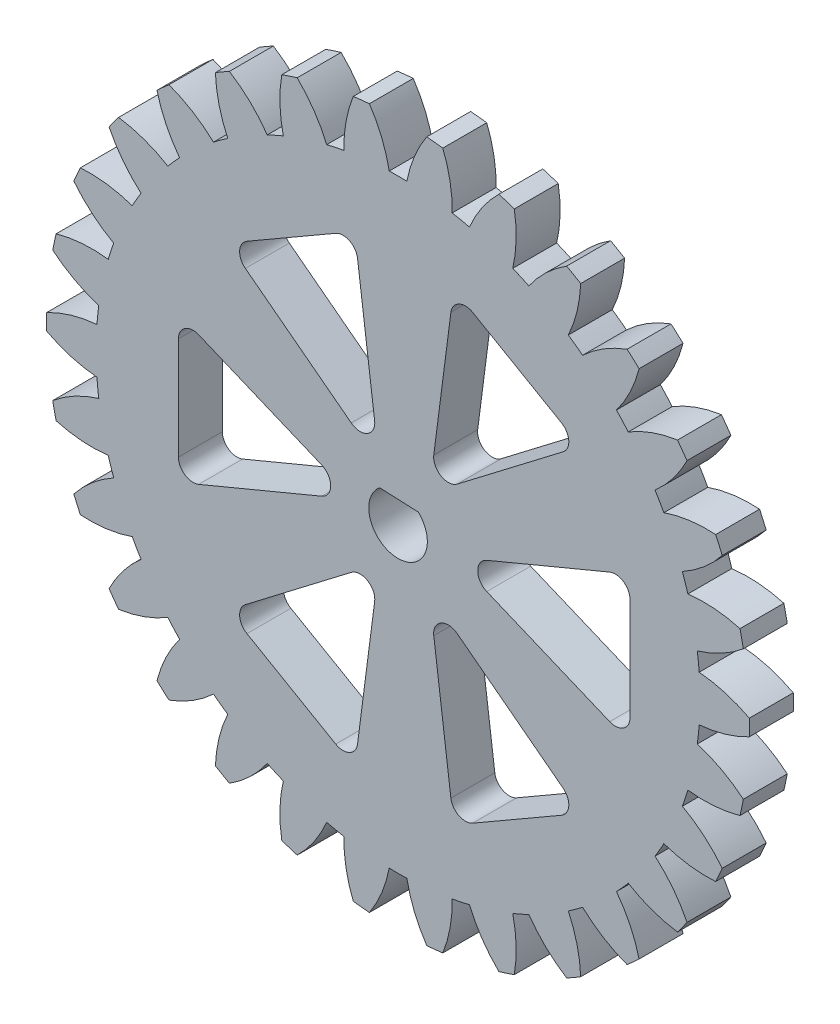
SolidWorks part; units mm, degrees
ref_plane "Front Plane" through (0, 0, 0) normal (0, 0, 1) x (1, 0, 0)
ref_plane "Top Plane" through (0, 0, 0) normal (0, 1, 0) x (1, 0, 0)
ref_plane "Right Plane" through (0, 0, 0) normal (1, 0, 0) x (0, 0, -1)
sketch "Sketch1" plane through (0, 0, 0) normal (0, 0, 1) x (1, 0, 0)
  circle A0 centre (0, 0) radius 24
  dimension "addendumDiameter" = 48
extrude "Boss-Extrude1" add sketch "Sketch1" along normal blind 3
sketch "Sketch2" plane through (0, 0, 3) normal (0, 0, 1) x (1, 0, 0)
  line L0 (0, 0) -> (0, 29.9865) construction
  line L1 (0, 0) -> (-2.0012, 19.0398) construction
  line L2 (-1.1705, 22.4695) -> (-2.3486, 22.3457) construction
  circle A0 centre (0, 0) radius 21.1431 construction
  circle A1 centre (0, 0) radius 22.5 construction
  circle A2 centre (0, 0) radius 20.625 construction
  arc A3 (-1.9581, 23.92) -> (1.9581, 23.92) centre (0, 0) cw
  circle A5 centre (0, 0) radius 24 construction
  arc A6 (-0.6019, 20.6162) -> (0.6019, 20.6162) centre (0, 0) cw
  arc A7 (-0.6019, 20.6162) -> (-1.9581, 23.92) centre (-9.4404, 18.9185) ccw
  arc A8 (0.6019, 20.6162) -> (1.9581, 23.92) centre (9.4404, 18.9185) cw
  dimension "dedendum" = 41.25
  dimension "Base" = 42.2862
  dimension "PitchDiameter" = 45
  dimension "D2" = 9
  dimension "D1" = 6
  dimension "D3" = 1.1781
extrude "Cut-Extrude1" cut sketch "Sketch2" against normal through all
pattern_circular "CirPattern1" count 30 over 360 about axis through (0, 0, 0) along (0, 0, 1) of "Cut-Extrude1"
sketch "Sketch3" plane through (0, 0, 3) normal (0, 0, 1) x (1, 0, 0)
  line L0 (-3, 0) -> (-15, -5)
  line L1 (-15, -5) -> (-15, 5)
  line L2 (-15, 5) -> (-3, 0)
  dimension "D1" = 10
  dimension "D2" = 12
  dimension "D3" = 3
extrude "Cut-Extrude2" cut sketch "Sketch3" against normal through all
fillet "Fillet5" radius 1 1 edges at (-15, -5, 1.5)
fillet "Fillet6" radius 1 1 edges at (-15, 5, 1.5)
fillet "Fillet7" radius 1 1 edges at (-3, 0, 1.5)
pattern_circular "CirPattern4" count 6 over 360 about axis through (0.4215, 0, 0) along (0, 0, 1) of "Cut-Extrude2", "Fillet5", "Fillet7", "Fillet6"
sketch "Sketch4" plane through (0, 0, 3) normal (0, 0, 1) x (1, 0, 0)
  line L0 (-1.2526, 1.5591) -> (1.3903, 1.4377)
  arc A0 (-1.2526, 1.5591) -> (1.3903, 1.4377) centre (0, 0) ccw
  dimension "D1" = 4
  dimension "D2" = 1.5
  dimension "D3" = 2.643
extrude "Cut-Extrude3" cut sketch "Sketch4" against normal through all
equation "\"module\"= 1.5"
equation "\"teeth\"= 30"
equation "\"pressureAngle\"= 20deg"
equation "\"gearThickness\"= 3"
equation "\"addendumfactor\"= 1"
equation "\"dedendumfactor\"= 1.25"
equation "\"pitch\"= 1 / \"module\""
equation "\"pitchDiameter\"= \"teeth\" / \"pitch\""
equation "\"addendum\"= \"addendumfactor\" / \"pitch\""
equation "\"dedendum\"= \"dedendumfactor\" / \"pitch\""
equation "\"addendumDiameter@Sketch1\"= \"pitchDiameter\" + 2 * \"addendum\""
equation "\"D1@Boss-Extrude1\"=\"gearThickness\""
equation "\"dedendum@Sketch2\"=\"pitchDiameter\"-2 * \"dedendum\""
equation "\"Base@Sketch2\"=\"pitchDiameter\" * cos(\"pressureAngle\" )"
equation "\"PitchDiameter@Sketch2\"=\"pitchDiameter\""
equation "\"D1@Sketch2\"= 180 / \"teeth\""
equation "\"D2@Sketch2\"= \"pitchDiameter\" / 5"
equation "\"D3@Sketch2\"=PI / 2 / \"pitch\" / 2"
